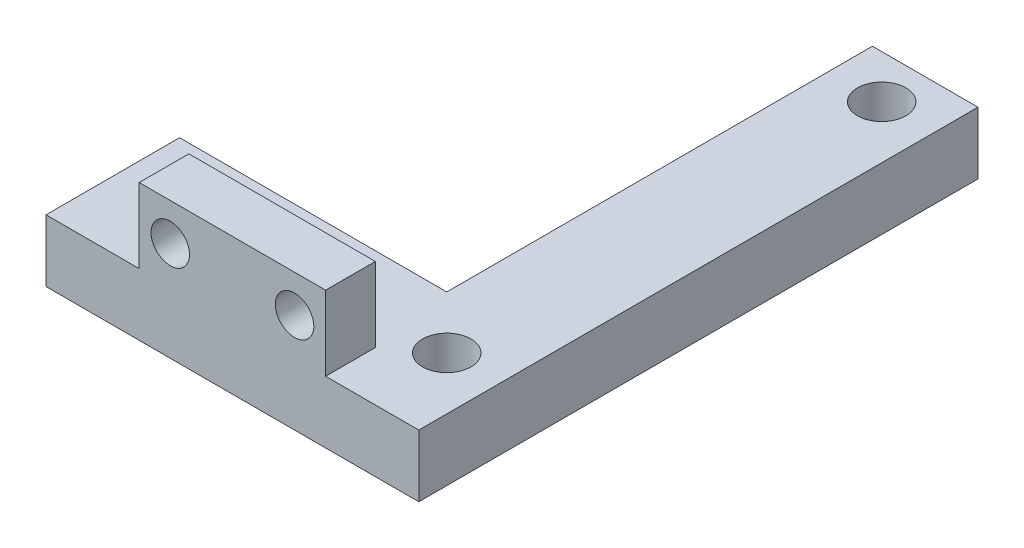
SolidWorks part; units mm, degrees
ref_plane "Front Plane" through (0, 0, 0) normal (0, 0, 1) x (1, 0, 0)
ref_plane "Top Plane" through (0, 0, 0) normal (0, 1, 0) x (1, 0, 0)
ref_plane "Right Plane" through (0, 0, 0) normal (1, 0, 0) x (0, 0, -1)
sketch "Sketch1" plane through (0, 0, 0) normal (0, 1, 0) x (1, 0, 0)
  line L1 (15, -22.5) -> (-15, -22.5)
  line L2 (15, -22.5) -> (15, 22.5)
  line L3 (15, 22.5) -> (-15, 22.5)
  line L4 (-15, -22.5) -> (-15, 22.5)
  line L5 (15, -22.5) -> (-15, 22.5) construction
  line L6 (15, 22.5) -> (-15, -22.5) construction
  point P0 (0, 0)
  dimension "D1" = 45
  dimension "D2" = 30
extrude "Boss-Extrude1" add sketch "Sketch1" along normal blind 5
sketch "Sketch2" plane through (0, 5, 0) normal (0, 1, 0) x (1, 0, 0)
  line L0 (15, -22.5) -> (15, 22.5) construction
  line L1 (15, 22.5) -> (-15, 22.5) construction
  line L2 (-15, 22.5) -> (-15, -11.75)
  line L3 (-15, 22.5) -> (-15, -22.5) construction
  line L4 (-15, -11.75) -> (6.5, -11.75)
  line L5 (6.5, -11.75) -> (6.5, 22.5)
  line L6 (6.5, 22.5) -> (-15, 22.5)
  circle A0 centre (10.75, 19) radius 1.95
  circle A1 centre (10.75, -16) radius 1.95
  circle A2 centre (-10.75, -16) radius 1.95
  dimension "D1" = 4.25
  dimension "D2" = 3.5
  dimension "D5" = 4.25
  dimension "D6" = 4.25
  dimension "D3" = 2
  dimension "D4" = 2
extrude "Cut-Extrude1" cut sketch "Sketch2" against normal through all
sketch "Sketch3" plane through (0, 5, 0) normal (0, 1, 0) x (1, 0, 0)
  line L0 (7.5, -22.5) -> (7.5, -18.5)
  line L1 (-15, -22.5) -> (15, -22.5) construction
  line L2 (7.5, -18.5) -> (-7.5, -18.5)
  line L3 (-7.5, -18.5) -> (-7.5, -22.5)
  line L4 (-7.5, -22.5) -> (7.5, -22.5)
  line L5 (-15, -11.75) -> (-15, -22.5) construction
  point P5 (0, -18.5)
  dimension "D1" = 15
  dimension "D2" = 15
  dimension "D3" = 4
extrude "Boss-Extrude2" add sketch "Sketch3" along normal blind 6
sketch "Sketch4" plane through (0, 0, 18.5) normal (0, 0, -1) x (-1, 0, 0)
  line L0 (-7.5, 11) -> (-7.5, 5) construction
  line L1 (-7.5, 11) -> (7.5, 11) construction
  circle A0 centre (-5, 8) radius 1.55
  circle A1 centre (5, 8) radius 1.55
  dimension "D1" = 2
  dimension "D2" = 2.5
  dimension "D3" = 3
extrude "Cut-Extrude2" cut sketch "Sketch4" against normal through all
